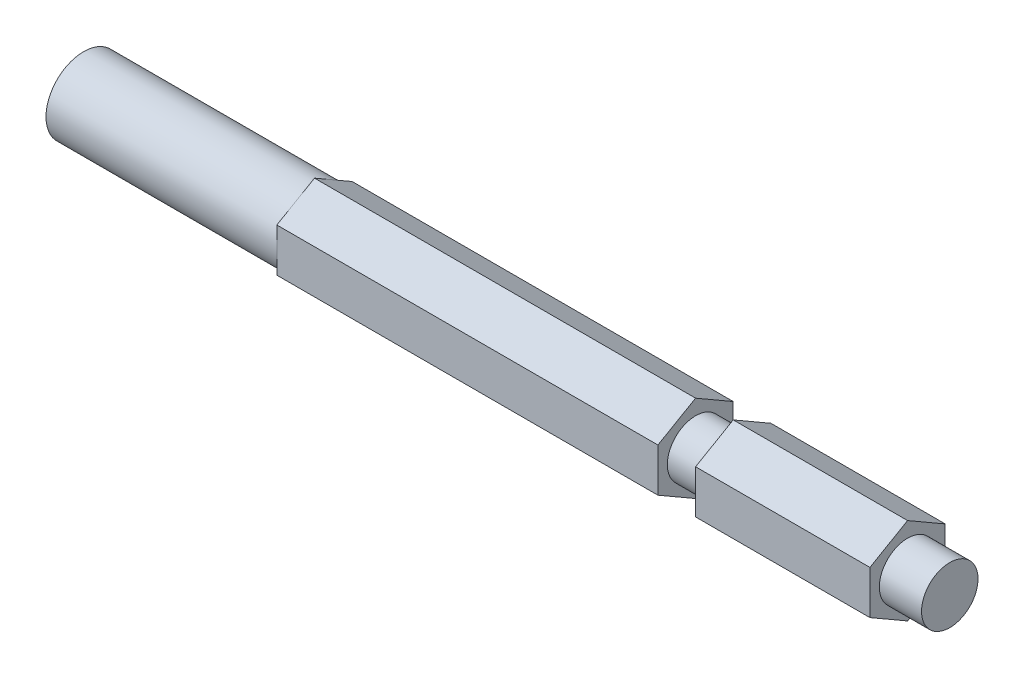
SolidWorks part; units mm, degrees
material "7075-T6 (SN)"
ref_plane "Front Plane" through (0, 0, 0) normal (0, 0, 1) x (1, 0, 0)
ref_plane "Top Plane" through (0, 0, 0) normal (0, 1, 0) x (1, 0, 0)
ref_plane "Right Plane" through (0, 0, 0) normal (1, 0, 0) x (0, 0, -1)
sketch "Sketch1" plane through (0, 0, 0) normal (1, 0, 0) x (0, 0, -1)
  circle A0 centre (0, 0) radius 6.35
  dimension "D1" = 12.7
extrude "Boss-Extrude1" add sketch "Sketch1" along normal blind 146.05
sketch "Sketch2" plane through (0, 0, 0) normal (-1, 0, 0) x (0, 0, 1)
  line L0 (-4.826, -4.127) -> (-4.826, 4.127)
  circle A0 centre (0, 0) radius 6.35 construction
  dimension "D1" = 4.826
extrude "Cut-Extrude1" cut sketch "Sketch2" against normal blind 25.4 and the other way through all
sketch "Sketch3" plane through (0, 0, 0) normal (0, 1, 0) x (1, 0, 0)
  line L1 (31.75, 0) -> (38.1, 0)
  line L2 (31.75, 0) -> (31.75, 12.7)
  line L3 (31.75, 12.7) -> (38.1, 12.7)
  line L4 (38.1, 0) -> (38.1, 12.7)
  dimension "D1" = 38.1
  dimension "D2" = 6.35
  dimension "D3" = 12.7
sketch "Sketch4" plane through (146.05, 0, 0) normal (1, 0, 0) x (0, 0, -1)
  line L1 (6.35, -3.6662) -> (6.35, 3.6662)
  line L2 (6.35, 3.6662) -> (0, 7.3323)
  line L3 (0, 7.3323) -> (-6.35, 3.6662)
  line L4 (-6.35, 3.6662) -> (-6.35, -3.6662)
  line L5 (-6.35, -3.6662) -> (0, -7.3323)
  line L6 (0, -7.3323) -> (6.35, -3.6662)
  circle A0 centre (0, 0) radius 6.35 construction
  point P1 (6.35, 0)
extrude "Boss-Extrude2" add sketch "Sketch4" against normal blind 100.0125 from offset 7.112 offset against normal yes
sketch "Sketch5" plane through (146.05, 0, 0) normal (1, 0, 0) x (0, 0, -1)
  circle A0 centre (0, 0) radius 4.7625
  circle A1 centre (0, 0) radius 6.35 construction
  circle A2 centre (0, 0) radius 6.35
  dimension "D1" = 9.525
extrude "Cut-Extrude2" cut sketch "Sketch5" against normal up to surface (7.112 mm away) up to face at (138.938, 3.1969, -5.5373)
sketch "Sketch6" plane through (146.05, 0, 0) normal (1, 0, 0) x (0, 0, -1)
  circle A0 centre (0, 0) radius 4.7625 construction
  circle A1 centre (0, 0) radius 4.7625
  circle A2 centre (0, 0) radius 19.8269
extrude "Cut-Extrude3" cut sketch "Sketch6" against normal blind 6.35 from offset 36.5125
